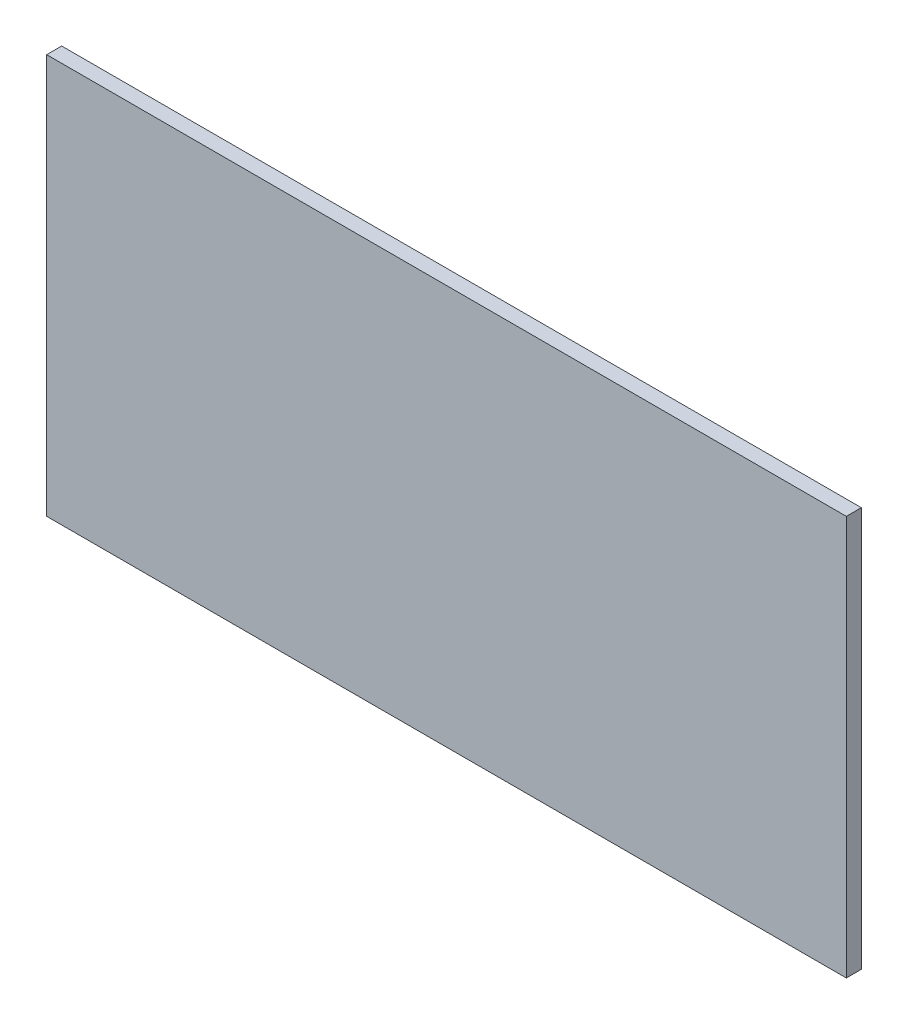
SolidWorks part; units mm, degrees
ref_plane "Front Plane" through (0, 0, 0) normal (0, 0, 1) x (1, 0, 0)
ref_plane "Top Plane" through (0, 0, 0) normal (0, 1, 0) x (1, 0, 0)
ref_plane "Right Plane" through (0, 0, 0) normal (1, 0, 0) x (0, 0, -1)
sketch "Sketch1" plane through (0, 0, 0) normal (0, 0, 1) x (1, 0, 0)
  line L1 (-66.3026, 44.9367) -> (93.6974, 44.9367)
  line L2 (-66.3026, 44.9367) -> (-66.3026, -35.0633)
  line L3 (-66.3026, -35.0633) -> (93.6974, -35.0633)
  line L4 (93.6974, 44.9367) -> (93.6974, -35.0633)
  dimension "D1" = 80
  dimension "D2" = 160
extrude "Boss-Extrude1" add sketch "Sketch1" along normal blind 3 contours L2 L1 L4 L3
